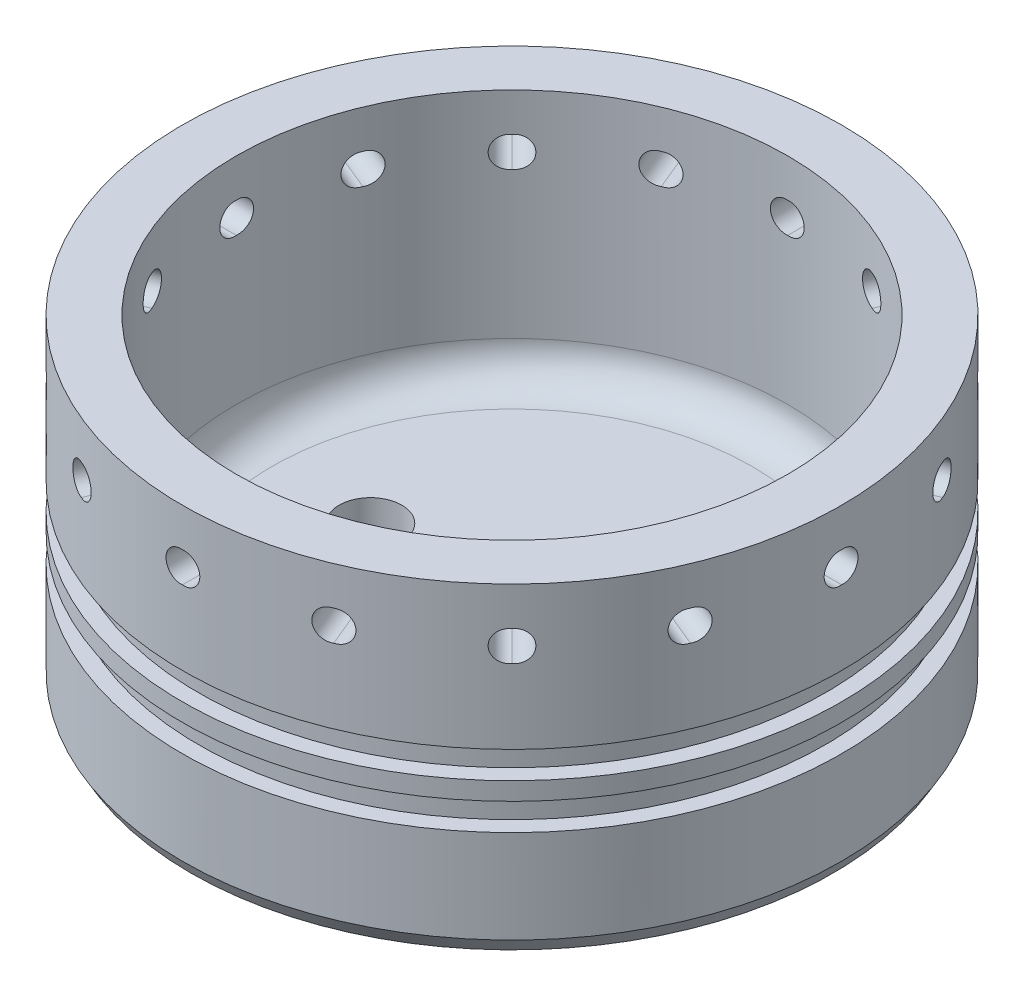
SolidWorks part; units mm, degrees
material "6061-T6 (SS)"
ref_plane "Front Plane" through (0, 0, 0) normal (0, 0, 1) x (1, 0, 0)
ref_plane "Top Plane" through (0, 0, 0) normal (0, 1, 0) x (1, 0, 0)
ref_plane "Right Plane" through (0, 0, 0) normal (1, 0, 0) x (0, 0, -1)
sketch "Sketch1" plane through (0, 0, 0) normal (0, 0, 1) x (1, 0, 0)
  line L1 (0, -9.525) -> (58.4454, -9.525)
  line L2 (58.4454, -9.525) -> (58.4454, 41.275) construction
  line L3 (0, 47.7012) -> (9.525, 47.7012)
  line L4 (58.4454, -9.525) -> (58.4454, 3.175)
  line L5 (58.4454, 3.175) -> (9.525, 3.175)
  line L6 (9.525, 3.175) -> (9.525, 47.7012)
  line L8 (0, -9.525) -> (0, 9.525)
  line L9 (0, 9.525) -> (2.8194, 9.525)
  line L10 (2.8194, 9.525) -> (2.8194, 14.3256)
  line L11 (2.8194, 14.3256) -> (0, 14.3256)
  line L15 (0, 14.3256) -> (0, 17.5006)
  line L16 (0, 17.5006) -> (2.8194, 17.5006)
  line L17 (2.8194, 17.5006) -> (2.8194, 22.3012)
  line L18 (2.8194, 22.3012) -> (0, 22.3012)
  line L19 (0, 22.3012) -> (0, 47.7012)
  dimension "D1" = 3.175
  dimension "D2" = 58.4454
  dimension "D3" = 12.7
  dimension "D4" = 19.05
  dimension "D5" = 4.8006
  dimension "D6" = 2.8194
  dimension "D10" = 25.4
  dimension "D11" = 9.525
revolve "Revolve1" add sketch "Sketch1" angle 360 about L2
ref_plane "HoleReferencePlane" through (0, 0, 58.4454) normal (0, 0, 1) x (1, 0, 0)
sketch "HoleReferencePoint" plane through (0, 0, 58.4454) normal (0, 0, 1) x (1, 0, 0)
  line L0 (107.3658, 47.7012) -> (9.525, 47.7012) construction
  point P0 (58.7375, 38.1762)
  dimension "D1" = 9.525
hole_wizard "ForwardClosureHoles" positions "Sketch3" profile "Sketch5" hole size "1/4-28" standard "ANSI Inch" end condition through all
sketch "Sketch3" plane through (0, 0, 58.4454) normal (0, 0, 1) x (1, 0, 0)
  point P0 (58.7375, 38.1762)
sketch "Sketch5" plane through (58.7375, 38.1762, 58.4454) normal (1, 0, 0) x (0, -1, 0)
  line L0 (0, 0) -> (0, 116.8908)
  line L1 (0, 116.8908) -> (2.7051, 116.8908)
  line L2 (2.7051, 116.8908) -> (2.7051, 0)
  line L5 (2.7051, 0) -> (0, 0)
  line L11 (0, -6.35) -> (0, 107.95) construction
  dimension "Thru Hole Dia." = 5.4102
  dimension "Thru Hole Depth" = 116.8908
sketch "Centerline" plane through (0, 0, 0) normal (0, 0, 1) x (1, 0, 0)
  line L0 (58.4454, 47.7012) -> (58.4454, -9.525) construction
  line L1 (116.8908, 47.7012) -> (0, 47.7012) construction
  line L2 (0, -9.525) -> (116.8908, -9.525) construction
pattern_circular "HolePattern" count 16 over 360 about axis through (58.4454, 47.7012, 0) along (0, -1, 0) of "ForwardClosureHoles"
ref_plane "HoleAlignmentPlane" through (0, 38.1762, 0) normal (0, 1, 0) x (1, 0, 0)
chamfer "Chamfer1" distance 2.54 angle 30 1 edges at (58.4454, -9.525, -58.4454)
fillet "Fillet1" radius 6.35 1 edges at (58.4454, 3.175, -48.9204)
sketch "Sketch7" plane through (0, 0, 0) normal (0, 1, 0) x (1, 0, 0)
  line L0 (58.7375, 0) -> (84.1375, 0)
  line L2 (58.7375, 0) -> (33.3375, 0)
  point P4 (33.3375, 0)
  point P5 (58.7375, 0)
  dimension "D1" = 25.4
  dimension "D2" = 25.4
hole_wizard "Pipe Tap Drill for 1/8 Tap1" positions "Sketch8" profile "Sketch9" hole size "1/8" standard "ANSI Inch" end condition through all
sketch "Sketch8" plane through (0, 3.175, 0) normal (0, 1, 0) x (1, 0, 0)
  point P0 (58.7375, 0)
sketch "Sketch9" plane through (58.7375, 3.175, 0) normal (1, 0, 0) x (0, 0, 1)
  line L0 (0, 0) -> (0, 12.7)
  line L1 (0, 12.7) -> (4.2164, 12.7)
  line L2 (4.2164, 12.7) -> (4.2164, 0)
  line L5 (4.2164, 0) -> (0, 0)
  line L11 (0, -6.35) -> (0, 107.95) construction
  dimension "Thru Hole Dia." = 8.4328
  dimension "Thru Hole Depth" = 12.7
hole_wizard "Pipe Tap Drill for 1/4 Tap1" positions "Sketch13" profile "Sketch14" hole size "1/4" standard "ANSI Inch" end condition through all
sketch "Sketch13" plane through (0, 3.175, 0) normal (0, 1, 0) x (1, 0, 0)
  point P0 (33.3375, 0)
sketch "Sketch14" plane through (33.3375, 3.175, 0) normal (1, 0, 0) x (0, 0, 1)
  line L0 (0, 0) -> (0, 12.7)
  line L1 (0, 12.7) -> (5.5626, 12.7)
  line L2 (5.5626, 12.7) -> (5.5626, 0)
  line L5 (5.5626, 0) -> (0, 0)
  line L11 (0, -6.35) -> (0, 107.95) construction
  dimension "Thru Hole Dia." = 11.1252
  dimension "Thru Hole Depth" = 12.7
